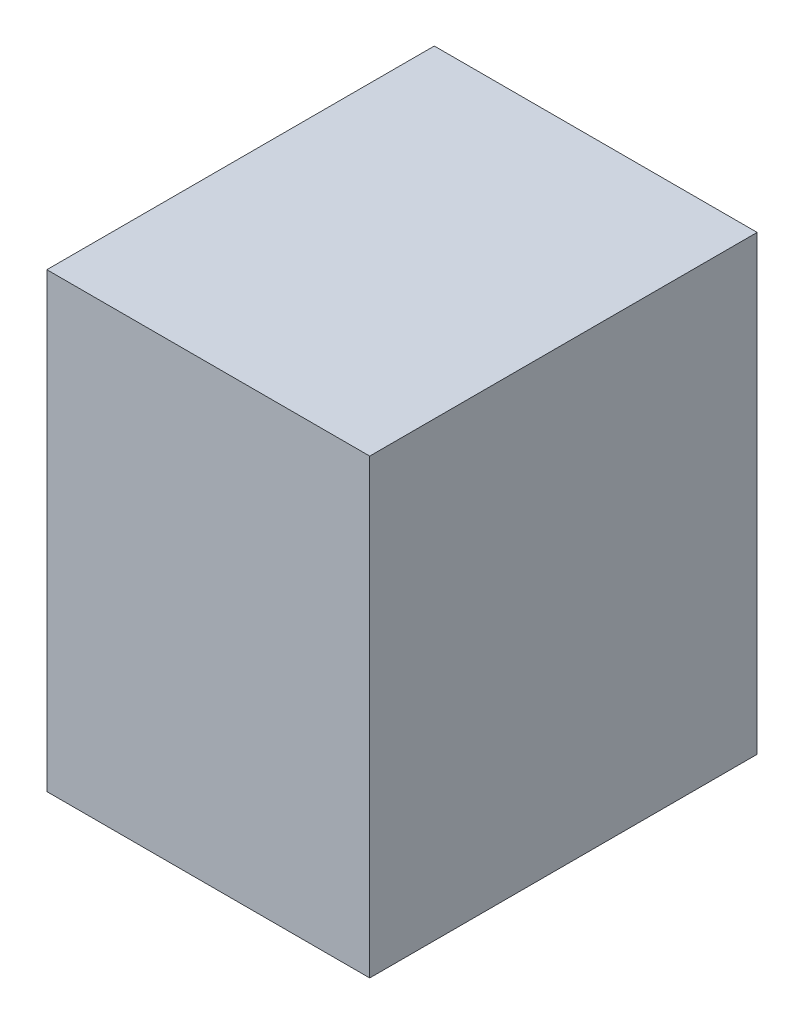
SolidWorks part; units mm, degrees
ref_plane "Ön Düzlem" through (0, 0, 0) normal (0, 0, 1) x (1, 0, 0)
ref_plane "Üst Düzlem" through (0, 0, 0) normal (0, 1, 0) x (1, 0, 0)
ref_plane "Sağ Düzlem" through (0, 0, 0) normal (1, 0, 0) x (0, 0, -1)
sketch "Çizim1" plane through (0, 0, 0) normal (0, 0, 1) x (1, 0, 0)
  line L1 (-65.3514, 35.9943) -> (-15.3514, 35.9943)
  line L2 (-65.3514, 35.9943) -> (-65.3514, -34.0057)
  line L3 (-65.3514, -34.0057) -> (-15.3514, -34.0057)
  line L4 (-15.3514, 35.9943) -> (-15.3514, -34.0057)
  dimension "D1" = 70
  dimension "D2" = 50
extrude "Yükseklik-Ekstrüzyon1" add sketch "Çizim1" along normal blind 60
